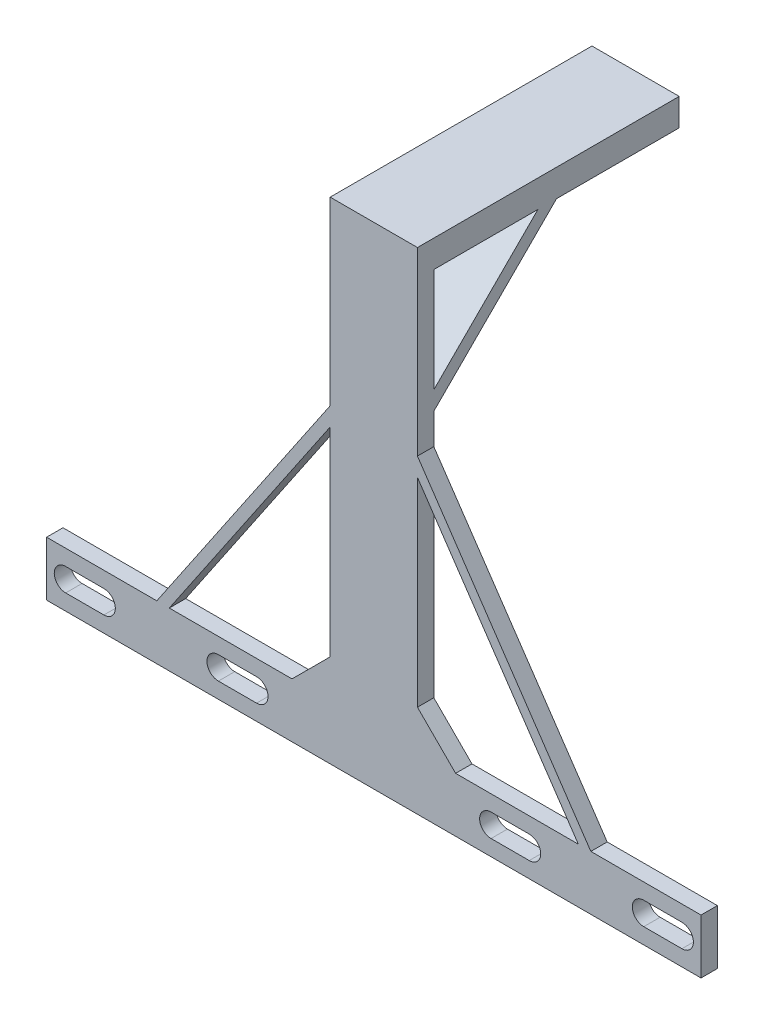
SolidWorks part; units mm, degrees
ref_plane "Front Plane" through (0, 0, 0) normal (0, 0, 1) x (1, 0, 0)
ref_plane "Top Plane" through (0, 0, 0) normal (0, 1, 0) x (1, 0, 0)
ref_plane "Right Plane" through (0, 0, 0) normal (1, 0, 0) x (0, 0, -1)
sketch "Sketch1" plane through (0, 0, 0) normal (0, 0, 1) x (1, 0, 0)
  line L0 (0, 0) -> (120, 0)
  line L1 (120, 0) -> (120, 10)
  line L2 (0, 0) -> (0, 10)
  line L4 (0, 10) -> (45, 10)
  line L5 (120, 10) -> (75, 10)
  line L6 (75, 10) -> (68, 17)
  line L8 (45, 10) -> (52, 17)
  line L9 (52, 17) -> (52, 40)
  line L10 (68, 17) -> (68, 40)
  line L11 (52, 90) -> (52, 40)
  line L12 (68, 90) -> (68, 40)
  line L13 (52, 90) -> (68, 90)
extrude "Boss-Extrude1" add sketch "Sketch1" along normal blind 3
sketch "Sketch2" plane through (0, 0, 3) normal (0, 0, 1) x (1, 0, 0)
  line L7 (3.5, 5) -> (10.5, 5) construction
  line L10 (3.5, 7.1) -> (10.5, 7.1)
  line L11 (3.5, 2.9) -> (10.5, 2.9)
  line L12 (31.5, 5) -> (38.5, 5) construction
  line L13 (31.5, 7.1) -> (38.5, 7.1)
  line L14 (31.5, 2.9) -> (38.5, 2.9)
  line L15 (81.5, 5) -> (88.5, 5) construction
  line L16 (81.5, 7.1) -> (88.5, 7.1)
  line L17 (81.5, 2.9) -> (88.5, 2.9)
  line L18 (116.5, 5) -> (109.5, 5) construction
  line L19 (116.5, 2.9) -> (109.5, 2.9)
  line L20 (116.5, 7.1) -> (109.5, 7.1)
  arc A2 (3.5, 7.1) -> (3.5, 2.9) centre (3.5, 5) ccw
  arc A3 (10.5, 2.9) -> (10.5, 7.1) centre (10.5, 5) ccw
  arc A4 (31.5, 7.1) -> (31.5, 2.9) centre (31.5, 5) ccw
  arc A5 (38.5, 2.9) -> (38.5, 7.1) centre (38.5, 5) ccw
  arc A6 (81.5, 7.1) -> (81.5, 2.9) centre (81.5, 5) ccw
  arc A7 (88.5, 2.9) -> (88.5, 7.1) centre (88.5, 5) ccw
  arc A8 (116.5, 2.9) -> (116.5, 7.1) centre (116.5, 5) ccw
  arc A9 (109.5, 7.1) -> (109.5, 2.9) centre (109.5, 5) ccw
  point P0 (0, 0)
  point P9 (7, 5)
  point P16 (35, 5)
  point P22 (85, 5)
  point P29 (113, 5)
  point P35 (0, 0)
  point P36 (0, 0)
  point P37 (0, 0)
  point P38 (0, 0)
  point P39 (0, 0)
extrude "Cut-Extrude1" cut sketch "Sketch2" against normal blind 3
sketch "Sketch4" plane through (0, 0, 0) normal (0, 0, -1) x (-1, 0, 0)
  line L0 (-52, 90) -> (-52, 17) construction
  line L1 (-68, 90) -> (-52, 90)
  line L2 (-68, 90) -> (-68, 85)
  line L3 (-68, 85) -> (-52, 85)
  line L4 (-52, 90) -> (-52, 85)
extrude "Boss-Extrude2" add sketch "Sketch4" along normal blind 45
sketch "Sketch7" plane through (52, 0, 0) normal (-1, 0, 0) x (0, 0, 1)
  line L0 (-22.5, 85) -> (0, 62.5)
  line L1 (-45, 85) -> (0, 85) construction
  line L2 (0, 85) -> (0, 17) construction
  line L3 (0, 62.5) -> (0, 65.9032)
  line L4 (0, 65.9032) -> (-19.0968, 85)
  line L5 (-19.0968, 85) -> (-22.5, 85)
extrude "Boss-Extrude3" add sketch "Sketch7" against normal blind 16
sketch "Sketch8" plane through (0, 0, 0) normal (0, 0, -1) x (-1, 0, 0)
  line L2 (-57.3423, 17) -> (-56.4933, 17)
  line L3 (-57.3423, 17) -> (-57.3423, 61.0712)
  line L4 (-57.3423, 61.0712) -> (-56.4933, 61.0712)
  line L5 (-56.4933, 17) -> (-56.4933, 61.0712)
  line L6 (-62.8925, 17) -> (-63.9223, 17)
  line L7 (-62.8925, 17) -> (-62.8925, 61.0712)
  line L8 (-62.8925, 61.0712) -> (-63.9223, 61.0712)
  line L9 (-63.9223, 17) -> (-63.9223, 61.0712)
extrude "Boss-Extrude4" add sketch "Sketch8" along normal blind 1
sketch "Sketch9" plane through (0, 0, 3) normal (0, 0, 1) x (1, 0, 0)
  line L0 (22.5, 10) -> (52, 53.5)
  line L1 (45, 10) -> (0, 10) construction
  line L2 (52, 90) -> (52, 17) construction
  line L3 (52, 53.5) -> (52, 56.8804)
  line L4 (52, 56.8804) -> (20.2075, 10)
  line L5 (20.2075, 10) -> (22.5, 10)
  line L6 (97.5, 10) -> (68, 53.5)
  line L7 (120, 10) -> (75, 10) construction
  line L8 (68, 17) -> (68, 90) construction
  line L9 (68, 53.5) -> (68, 56.8804)
  line L10 (68, 56.8804) -> (99.7925, 10)
  line L11 (99.7925, 10) -> (97.5, 10)
extrude "Boss-Extrude5" add sketch "Sketch9" against normal blind 3
